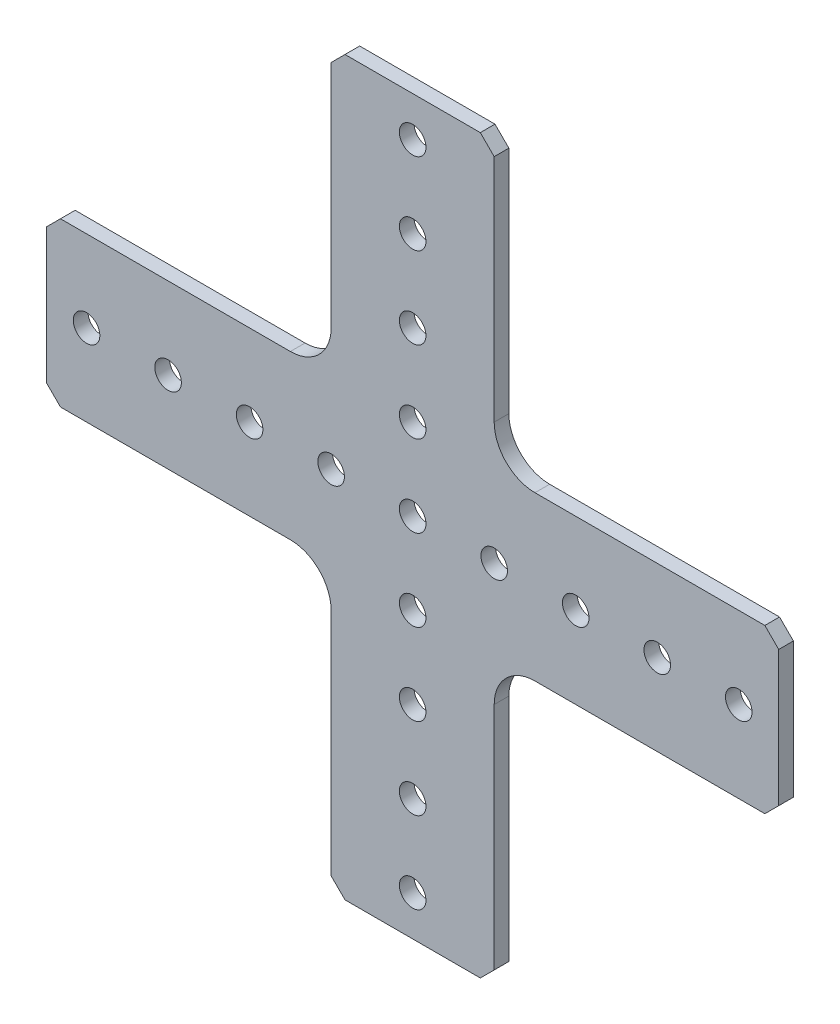
SolidWorks part; units mm, degrees
ref_plane "Front Plane" through (0, 0, 0) normal (0, 0, 1) x (1, 0, 0)
ref_plane "Top Plane" through (0, 0, 0) normal (0, 1, 0) x (1, 0, 0)
ref_plane "Right Plane" through (0, 0, 0) normal (1, 0, 0) x (0, 0, -1)
ref_plane "Plane1" through (0, 0, 2.286) normal (0, 0, 1) x (1, 0, 0)
sketch "Sketch1" plane through (0, 0, 2.286) normal (0, 0, 1) x (1, 0, 0)
  line L0 (57.023, 10.541) -> (54.864, 12.7)
  line L1 (54.864, 12.7) -> (19.05, 12.7)
  line L2 (12.7, 19.05) -> (12.7, 54.864)
  line L3 (12.7, 54.864) -> (10.541, 57.023)
  line L4 (10.541, 57.023) -> (-10.541, 57.023)
  line L5 (-10.541, 57.023) -> (-12.7, 54.864)
  line L6 (-12.7, 54.864) -> (-12.7, 19.05)
  line L7 (-19.05, 12.7) -> (-54.864, 12.7)
  line L8 (-54.864, 12.7) -> (-57.023, 10.541)
  line L9 (-57.023, 10.541) -> (-57.023, -10.541)
  line L10 (-57.023, -10.541) -> (-54.864, -12.7)
  line L11 (-54.864, -12.7) -> (-19.05, -12.7)
  line L12 (-12.7, -19.05) -> (-12.7, -54.864)
  line L13 (-12.7, -54.864) -> (-10.541, -57.023)
  line L14 (-10.541, -57.023) -> (10.541, -57.023)
  line L15 (10.541, -57.023) -> (12.7, -54.864)
  line L16 (12.7, -54.864) -> (12.7, -19.05)
  line L17 (19.05, -12.7) -> (54.864, -12.7)
  line L18 (54.864, -12.7) -> (57.023, -10.541)
  line L19 (57.023, -10.541) -> (57.023, 10.541)
  arc A0 (19.05, 12.7) -> (12.7, 19.05) centre (19.05, 19.05) cw
  arc A1 (-12.7, 19.05) -> (-19.05, 12.7) centre (-19.05, 19.05) cw
  arc A2 (-19.05, -12.7) -> (-12.7, -19.05) centre (-19.05, -19.05) cw
  arc A3 (12.7, -19.05) -> (19.05, -12.7) centre (19.05, -19.05) cw
  circle A4 centre (0, 12.7) radius 2.0701
  circle A5 centre (0, 38.1) radius 2.0701
  circle A6 centre (-12.7, 0) radius 2.0701
  circle A7 centre (-38.1, 0) radius 2.0701
  circle A8 centre (50.8, 0) radius 2.0701
  circle A9 centre (0, -38.1) radius 2.0701
  circle A10 centre (0, -12.7) radius 2.0701
  circle A11 centre (25.4, 0) radius 2.0701
  circle A12 centre (0, 0) radius 2.0701
  circle A13 centre (12.7, 0) radius 2.0701
  circle A14 centre (38.1, 0) radius 2.0701
  circle A15 centre (0, -25.4) radius 2.0701
  circle A16 centre (0, -50.8) radius 2.0701
  circle A17 centre (-50.8, 0) radius 2.0701
  circle A18 centre (-25.4, 0) radius 2.0701
  circle A19 centre (0, 50.8) radius 2.0701
  circle A20 centre (0, 25.4) radius 2.0701
extrude "Boss-Extrude1" add sketch "Sketch1" against normal blind 2.286
